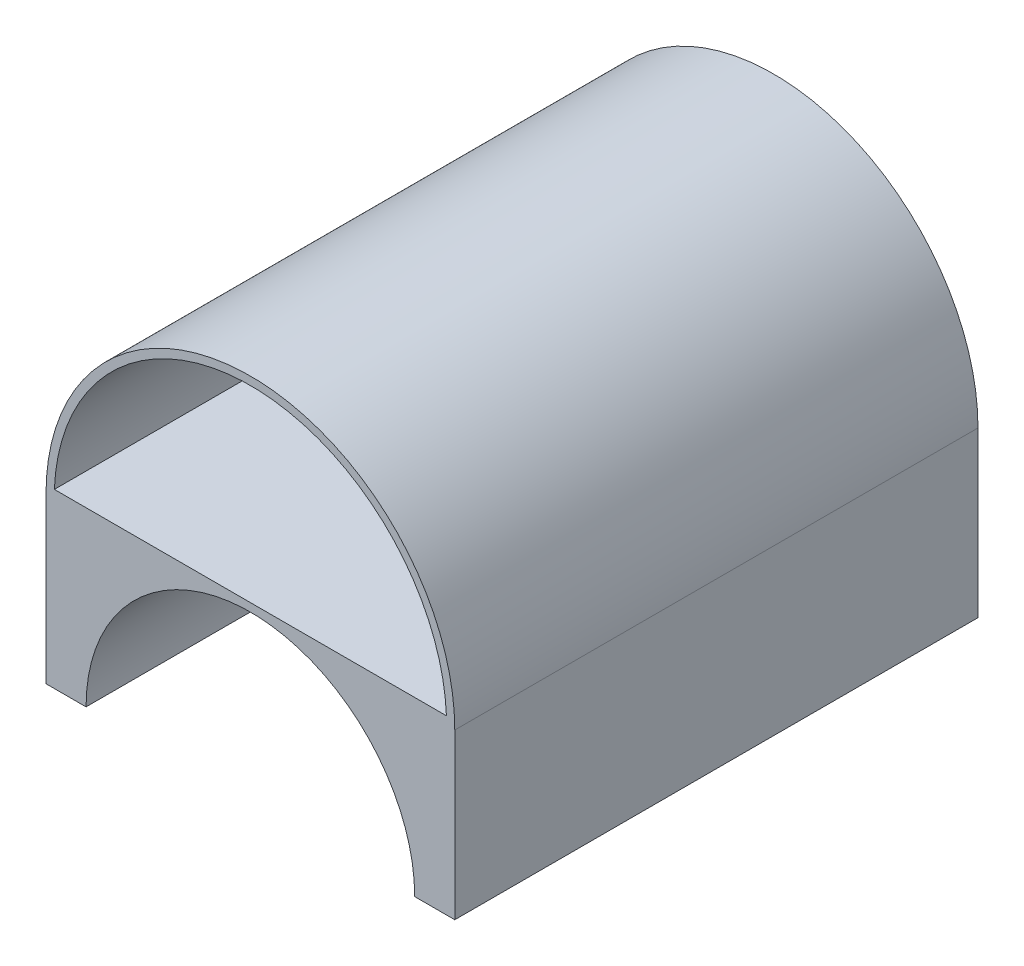
SolidWorks part; units mm, degrees
ref_plane "Front Plane" through (0, 0, 0) normal (0, 0, 1) x (1, 0, 0)
ref_plane "Top Plane" through (0, 0, 0) normal (0, 1, 0) x (1, 0, 0)
ref_plane "Right Plane" through (0, 0, 0) normal (1, 0, 0) x (0, 0, -1)
sketch "Sketch1" plane through (0, 0, 0) normal (0, 0, 1) x (1, 0, 0)
  line L0 (-31.75, 0) -> (31.75, 0)
  arc A0 (-31.75, 0) -> (31.75, 0) centre (0, 0) cw
  point P2 (0, 0)
  point P6 (0, 31.75)
  dimension "D1" = 0
  dimension "D2" = 31.75
  dimension "2.4" = 63.5
extrude "Boss-Extrude1" add sketch "Sketch1" against normal blind 81.28
shell "Shell2" thickness 1.27
sketch "Sketch5" plane through (0, 0, 0) normal (0, 0, 1) x (1, 0, 0)
  line L1 (-31.75, 0) -> (-31.75, -25.527)
  line L2 (-31.75, -25.527) -> (-25.527, -25.527)
  line L3 (25.527, -25.527) -> (31.75, -25.527)
  line L4 (31.75, -25.527) -> (31.75, 0)
  line L5 (31.75, 0) -> (-31.75, 0)
  arc A0 (25.527, -25.527) -> (-25.527, -25.527) centre (0, -25.527) ccw
  point P1 (0, 0)
  line M4 (-31.75, 0) -> (31.75, 0)
  dimension "D1" = 51.054
  dimension "D2" = 0
  dimension "D4" = 25.527
  dimension "D3" = 0
  dimension "D5" = 6.223
extrude "Boss-Extrude2" add sketch "Sketch5" against normal blind 81.28 contours A0 L1 L2 M4 | A0 L3 L4 L5
